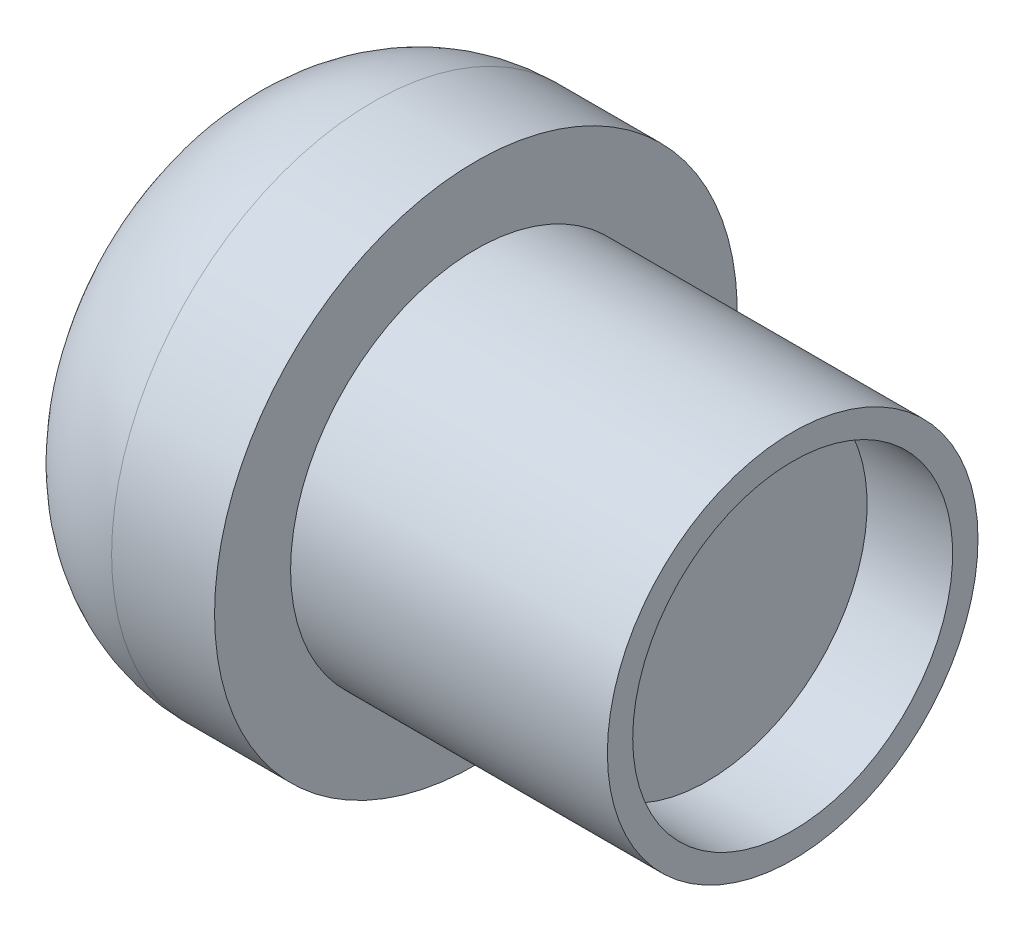
SolidWorks part; units mm, degrees
ref_plane "Ebene vorne" through (0, 0, 0) normal (0, 0, 1) x (1, 0, 0)
ref_plane "Ebene oben" through (0, 0, 0) normal (0, 1, 0) x (1, 0, 0)
ref_plane "Ebene rechts" through (0, 0, 0) normal (1, 0, 0) x (0, 0, -1)
sketch "Skizze1" plane through (0, 0, 0) normal (0, 0, 1) x (1, 0, 0)
  line L0 (0, 0) -> (-10, 0)
  line L1 (-10, 0) -> (-10, 2.4)
  line L2 (-10, 2.4) -> (-13.25, 2.4)
  line L3 (-18.25, -2.6) -> (-18.25, -5.85)
  line L4 (-18.25, -5.85) -> (-2.7, -5.85)
  line L5 (0, -0.8) -> (0, 0)
  line L6 (-27.303, -5.85) -> (-2.7, -5.85) construction
  line L7 (0, -0.8) -> (-2.7, -0.8)
  line L8 (-2.7, -0.8) -> (-2.7, -5.85)
  arc A0 (-13.25, 2.4) -> (-18.25, -2.6) centre (-13.25, -2.6) ccw
  point P11 (-18.25, 2.4)
  dimension "D5" = 5
  dimension "D1" = 5.85
  dimension "D2" = 8.25
  dimension "D3" = 10
  dimension "D4" = 8.25
  dimension "D6" = 5.05
  dimension "D7" = 2.7
revolve "Rotation1" add sketch "Skizze1" angle 360 about L6
